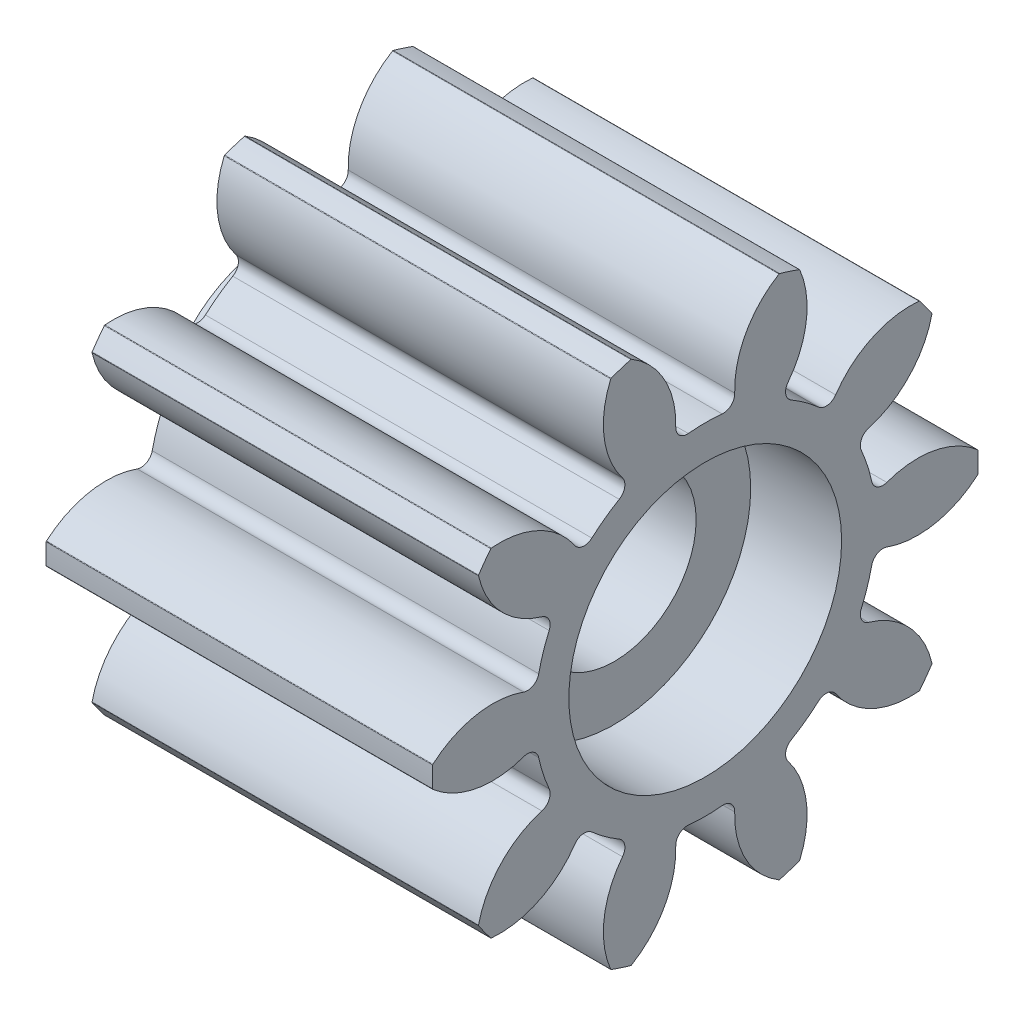
SolidWorks part; units mm, degrees
ref_plane "Plane1" through (0, 0, 0) normal (0, 0, 1) x (1, 0, 0)
ref_plane "Plane2" through (0, 0, 0) normal (0, 1, 0) x (1, 0, 0)
ref_plane "Plane3" through (0, 0, 0) normal (1, 0, 0) x (0, 0, -1)
sketch "HoldingSke" plane through (0, 0, 0) normal (0, 1, 0) x (1, 0, 0)
  line L0 (0, 0) -> (0.9848, -0.1736)
  line L1 (-15, 0) -> (100, 0) construction
  line L2 (0, 0) -> (-2.1039, 2.3779)
  line L3 (0, 0) -> (-11.863, 4.5341)
  line L4 (0, 0) -> (8.5048, 1.4996)
  line L5 (0, 0) -> (-46.8476, -17.4728)
  line L6 (0, 0) -> (-8.2896, -5.593)
  line L7 (-2.1039, 2.3779) -> (8.6586, 51.2059)
  line L8 (-76.2, 54.61) -> (-75.7, 54.61)
  line L9 (-67.7845, 28.3722) -> (-49.3413, 33.142)
  line L10 (-76.2, 71.12) -> (104.1128, 71.12)
  line L11 (0, 0) -> (-10, 0)
  line L12 (-76.2, 101.6) -> (-76.162, 101.6)
  line L13 (24.9733, 27.94) -> (52.9518, 28.4284)
  line L14 (24.9733, 27.94) -> (24.9743, 27.94)
  line L15 (24.9733, 27.94) -> (100.4006, 29.5858)
  line L16 (-63.627, -1) -> (-12.827, -1)
  circle A0 centre (0, 0) radius 1.5
  circle A1 centre (0, 0) radius 3.749
  circle A2 centre (0, 0) radius 37.5
  circle A3 centre (0, 0) radius 1.5
  dimension "MHD" = 7.498
  dimension "Hub_dia" = 75
  dimension "Bore" = 3
  dimension "MBD" = 3
  dimension "Num_teeth" = 10
  dimension "Pitch" = 1
  dimension "Overall_len" = 50
  dimension "Show_teeth" = 10
  dimension "Thickness" = 10
  dimension "OAL" = 50.0001
  dimension "T_dim" = 0.5
  dimension "Ap" = 14.5
  dimension "H" = 19.05
  dimension "Pitch_radius" = 180.3128
  dimension "Width" = 10
  dimension "Backlash" = 0.038
  dimension "Addendum_fac" = 1
  dimension "Dedendum_fac" = 1.25
  dimension "Clearance_fac" = 0.25
  dimension "Dedendum_add" = 0.001
  dimension "Module" = 1
sketch "BasProSke" plane through (0, 0, 0) normal (0, 1, 0) x (1, 0, 0)
  line L0 (-10, 0) -> (60, 0) construction
  line L1 (0, 0) -> (0, 6)
  line L2 (0, 0) -> (8.5, 0)
  line L3 (8.5, 0) -> (8.5, 6)
  line L4 (8.5, 6) -> (0, 6)
  dimension "Thickness" = 8.5
  dimension "Diameter" = 12
revolve "Base-Revolve" add sketch "BasProSke" angle 360 about L0
sketch "TooCutSke" plane through (0, 0, 0) normal (1, 0, 0) x (0, 0, -1)
  line L1 (0, 0) -> (0, 107) construction
  line L2 (0, 0) -> (-0.8485, 4.9275) construction
  line L3 (0, 0) -> (-3.0584, 9.4126) construction
  line L4 (-0.8485, 4.9275) -> (-1.5292, 4.7063) construction
  arc A0 (0.6809, 3.6866) -> (-0.6809, 3.6866) centre (0, 0) ccw
  arc A1 (1.66, 5.7922) -> (-1.66, 5.7922) centre (0, 0) ccw
  circle A2 centre (0, 0) radius 5 construction
  circle A3 centre (0, 0) radius 4.8407 construction
  arc A4 (-0.6809, 3.6866) -> (-1.66, 5.7922) centre (-2.6471, 4.0528) ccw
  arc A5 (1.66, 5.7922) -> (0.6809, 3.6866) centre (2.6471, 4.0528) ccw
  dimension "Root_dia" = 7.498
  dimension "Overcut_dia" = 12.0508
  dimension "Pitch_dia" = 10
  dimension "Base_dia" = 9.6815
  dimension "Flank_rad" = 2
  dimension "Half_ang" = 18
  dimension "Half_CT" = 0.7157
extrude "ToothCut" cut sketch "TooCutSke" along normal through all
fillet "Breaks" radius 0.02 2 edges at (4.25, 5.7745, -1.6294) (4.25, 5.7745, 1.6294)
fillet "RootFillets" radius 0.251 2 edges at (4.25, 3.6866, -0.6809) (4.25, 3.6866, 0.6809)
pattern_circular "TeethCuts" count 10 every 36 about axis through (-10, 0, 0) along (1, 0, 0) of "ToothCut", "RootFillets", "Breaks"
sketch "HubNeaOneSke" plane through (0, 0, 0) normal (-1, 0, 0) x (0, 0, 1)
  circle A0 centre (0, 0) radius 3.749
  dimension "Diameter" = 7.498
extrude "HubNearOne" [suppressed] add sketch "HubNeaOneSke" along normal blind 41.5001
sketch "HubNeaBotSke" plane through (0, 0, 0) normal (-1, 0, 0) x (0, 0, 1)
  circle A0 centre (0, 0) radius 3.749
  dimension "Diameter" = 7.498
extrude "HubNearBoth" [suppressed] add sketch "HubNeaBotSke" along normal blind 20.75
ref_plane "FarPln" through (8.5, 0, 0) normal (1, 0, 0) x (0, 0, -1)
sketch "HubFarSke" plane through (8.5, 0, 0) normal (1, 0, 0) x (0, 0, -1)
  circle A0 centre (0, 0) radius 3.749
  dimension "Diameter" = 7.498
extrude "HubFar" [suppressed] add sketch "HubFarSke" along normal blind 20.75
sketch "BorSke" plane through (0, 0, 0) normal (1, 0, 0) x (0, 0, -1)
  circle A0 centre (0, 0) radius 1.8
  dimension "Diameter" = 3.6
extrude "Bore" cut sketch "BorSke" along normal mid plane 100.0001
sketch "KeySke" plane through (0, 0, 0) normal (1, 0, 0) x (0, 0, -1)
  line L0 (-0.6, 0) -> (-0.6, 2)
  line L1 (-0.6, 2) -> (0.6, 2)
  line L2 (0.6, 2) -> (0.6, 0)
  line L3 (0, 0) -> (0, 34) construction
  line L4 (-0.6, 0) -> (0.6, 0)
  dimension "Offset" = 2
  dimension "Width" = 1.2
extrude "Keyway" [suppressed] cut sketch "KeySke" along normal mid plane 100.0001
pattern_circular "Keyway2" [suppressed] count 2 every 90 about axis through (-10, 0, 0) along (1, 0, 0)
sketch "Sketch3" plane through (0, 0, 0) normal (-1, 0, 0) x (0, 0, 1)
  circle A0 centre (0, 0) radius 2.5
  circle A1 centre (0, 0) radius 1.8 construction
  circle A2 centre (0, 0) radius 1.8
  dimension "D1" = 5
extrude "Boss-Extrude1" add sketch "Sketch3" along normal blind 1
sketch "Sketch4" plane through (8.5, 0, 0) normal (1, 0, 0) x (0, 0, -1)
  circle A0 centre (0, 0) radius 3
  point P2 (0, 0)
  dimension "D1" = 6
extrude "Cut-Extrude2" cut sketch "Sketch4" against normal blind 2
equation "' \"Module@HoldingSke\" = 6.35"
equation "' \"Num_teeth@HoldingSke\" = 12"
equation "' \"Ap@HoldingSke\" =  20"
equation "' \"Ap@HoldingSke\" = 20"
equation "' \"Width@HoldingSke\" = 0.5 * 25.4"
equation "' \"Hub_dia@HoldingSke\"= 1 * 25.4"
equation "' \"Hub_dia@HoldingSke\" = 1 * 25.4"
equation "' \"Overall_len@HoldingSke\" = 1.0 * 25.4"
equation "' \"Bore@HoldingSke\" = 0.75 * 25.4"
equation "' \"T_dim@HoldingSke\" = 0.1 * 25.4"
equation "' \"Width@KeySke\" = 0.25 * 25.4"
equation "' \"Show_teeth@HoldingSke\" = 13"
equation "' \"Backlash@HoldingSke\" = 0.009 * 25.4"
equation "' \"Addendum_fac@HoldingSke\" = 1.0"
equation "' \"Dedendum_fac@HoldingSke\" = 1.25"
equation "' \"Dedendum_add@HoldingSke\" = 0.00005 * 25.4"
equation "' \"Clearance_fac@HoldingSke\" = 0.25"
equation "\"Pitch@HoldingSke\" = 1 / \"Module@HoldingSke\""
equation "\"Overcut_dia@TooCutSke\" = (\"Num_teeth@HoldingSke\" + 2 * \"Addendum_fac@HoldingSke\") / \"Pitch@HoldingSke\" + 0.002 * 25.4"
equation "\"Pitch_dia@TooCutSke\" = \"Num_teeth@HoldingSke\" / \"Pitch@HoldingSke\""
equation "\"Base_dia@TooCutSke\" = \"Num_teeth@HoldingSke\" / \"Pitch@HoldingSke\" * cos((\"Ap@HoldingSke\"  * 3.14159265 / 180))"
equation "\"Root_dia@TooCutSke\" = (\"Num_teeth@HoldingSke\" + 2) / \"Pitch@HoldingSke\" - 2 * (\"Addendum_fac@HoldingSke\" + \"Dedendum_fac@HoldingSke\") / \"Pitch@HoldingSke\" - \"Dedendum_add@HoldingSke\" * 2"
equation "\"Half_ang@TooCutSke\" = 180 / \"Num_teeth@HoldingSke\""
equation "\"Half_CT@TooCutSke\" = \"Num_teeth@HoldingSke\" / \"Pitch@HoldingSke\" * sin((3.14159265 / 2 / \"Num_teeth@HoldingSke\")) / 2 - 7 * \"Backlash@HoldingSke\" / 4"
equation "\"Flank_rad@TooCutSke\" = \"Num_teeth@HoldingSke\" / \"Pitch@HoldingSke\" / 5"
equation "\"Radius@RootFillets\" = \"Clearance_fac@HoldingSke\" / \"Pitch@HoldingSke\" + \"Dedendum_add@HoldingSke\""
equation "\"Break_rad@Breaks\" = 0.02 / \"Pitch@HoldingSke\""
equation "\"Thickness@HoldingSke\" = \"Width@HoldingSke\""
equation "\"OAL@HoldingSke\" = \"Thickness@HoldingSke\""
equation "\"MHD@HoldingSke\" = (\"Num_teeth@HoldingSke\" + 2) / \"Pitch@HoldingSke\" - 2 * (\"Addendum_fac@HoldingSke\" + \"Dedendum_fac@HoldingSke\")  / \"Pitch@HoldingSke\" - \"Dedendum_add@HoldingSke\" * 2"
equation "\"MBD@HoldingSke\" = (\"Num_teeth@HoldingSke\" + 2) / \"Pitch@HoldingSke\" - 2 * (\"Addendum_fac@HoldingSke\" + \"Dedendum_fac@HoldingSke\")  / \"Pitch@HoldingSke\" - \"Dedendum_add@HoldingSke\" * 2 - 0.002 * 25.4"
equation "\"MHD@HoldingSke\" = ((sgn( \"MHD@HoldingSke\" - \"Hub_dia@HoldingSke\" )-1)*( \"MHD@HoldingSke\" - \"Hub_dia@HoldingSke\" ))/-2+ \"Hub_dia@HoldingSke\""
equation "\"MBD@HoldingSke\" = ((sgn( \"MBD@HoldingSke\" - \"Bore@HoldingSke\" )-1)*( \"MBD@HoldingSke\" - \"Bore@HoldingSke\" ))/-2+ \"Bore@HoldingSke\""
equation "\"OAL@HoldingSke\" = ((sgn( \"OAL@HoldingSke\" - \"Overall_len@HoldingSke\" )+1)*( \"OAL@HoldingSke\" - \"Overall_len@HoldingSke\" ))/2 + \"Overall_len@HoldingSke\" + 0.000002 * 25.4"
equation "\"Num_teeth@TeethCuts\" = int( \"Show_teeth@HoldingSke\" ) + 1"
equation "\"Num_teeth@TeethCuts\" = ((sgn( \"Num_teeth@TeethCuts\" - \"Num_teeth@HoldingSke\" )-1)*( \"Num_teeth@TeethCuts\" - \"Num_teeth@HoldingSke\" ))/-2+ \"Num_teeth@HoldingSke\""
equation "\"Num_teeth@TeethCuts\" = ((sgn( \"Num_teeth@TeethCuts\" - 2.0)+1)*( \"Num_teeth@TeethCuts\" - 2.0))/2 +2.0"
equation "\"Angle@TeethCuts\" = 360.0 / \"Num_teeth@HoldingSke\""
equation "\"Diameter@BasProSke\" = (\"Num_teeth@HoldingSke\" + 2 * \"Addendum_fac@HoldingSke\") / \"Pitch@HoldingSke\""
equation "' \"Fillet_rad@BasProSke\" =  \"Thickness@HoldingSke\" * 0.05"
equation "' \"Fillet_rad@BasProSke\" = \"Thickness@HoldingSke\" * 0.05"
equation "\"MHD@HoldingSke\" = ((sgn( \"MHD@HoldingSke\" - \"Root_dia@TooCutSke\" )-1)*( \"MHD@HoldingSke\" - \"Root_dia@TooCutSke\" ))/-2+ \"Root_dia@TooCutSke\""
equation "\"Diameter@HubNeaOneSke\" = \"MHD@HoldingSke\""
equation "\"Length@HubNearOne\" = \"OAL@HoldingSke\" - \"Thickness@BasProSke\""
equation "\"Diameter@HubNeaBotSke\" = \"MHD@HoldingSke\""
equation "\"Length@HubNearBoth\" = ( \"OAL@HoldingSke\" - \"Thickness@BasProSke\" ) / 2.0"
equation "\"Thickness@FarPln\" = \"Thickness@BasProSke\""
equation "\"Diameter@HubFarSke\" = \"MHD@HoldingSke\""
equation "\"Length@HubFar\" = ( \"OAL@HoldingSke\" - \"Thickness@BasProSke\" ) / 2.0"
equation "\"D1@Bore\" = \"OAL@HoldingSke\" * 2.0"
equation "\"D1@Keyway\" = \"OAL@HoldingSke\" * 2.0"
equation "\"Offset@KeySke\" = \"T_dim@HoldingSke\" + \"MBD@HoldingSke\" / 2.0"
